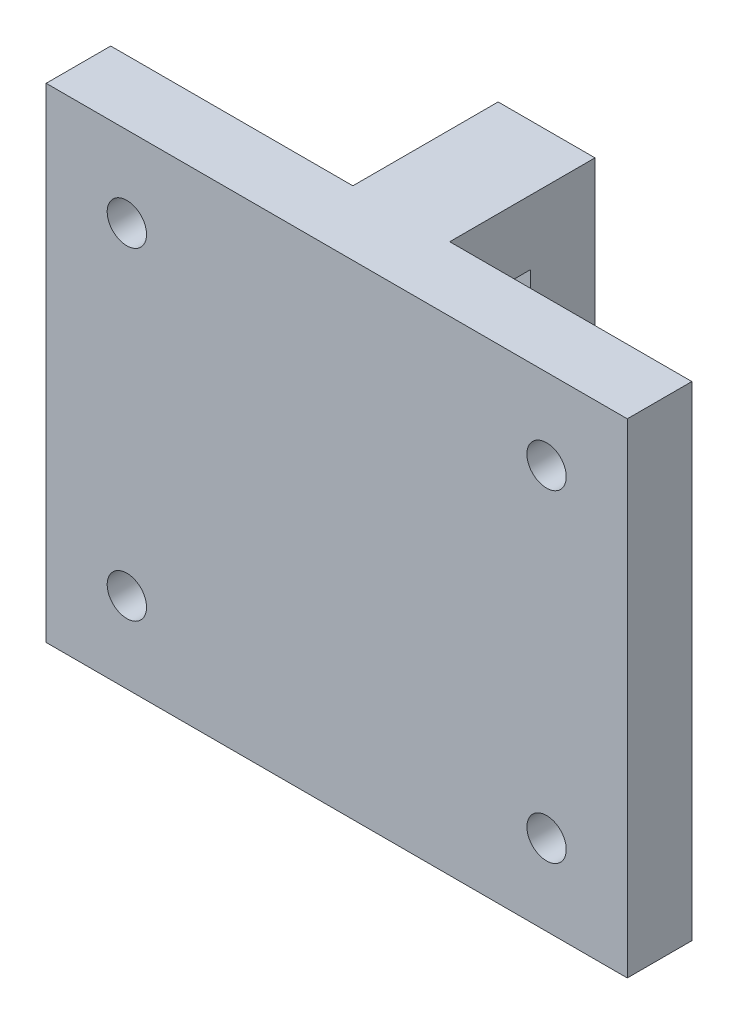
SolidWorks part; units mm, degrees
ref_plane "Front Plane" through (0, 0, 0) normal (0, 0, 1) x (1, 0, 0)
ref_plane "Top Plane" through (0, 0, 0) normal (0, 1, 0) x (1, 0, 0)
ref_plane "Right Plane" through (0, 0, 0) normal (1, 0, 0) x (0, 0, -1)
sketch "Sketch1" plane through (0, 0, 0) normal (1, 0, 0) x (0, 0, -1)
  line L1 (0, 0) -> (4, 0)
  line L2 (0, 0) -> (0, 30)
  line L3 (0, 30) -> (13, 30)
  line L4 (4, 0) -> (4, 26)
  line L5 (0, 30) -> (13, 30)
  line L7 (4, 26) -> (9, 26)
  line L8 (13, 30) -> (13, 16)
  line L10 (13, 30) -> (13, 16)
  line L11 (13, 16) -> (9, 16)
  line L12 (9, 26) -> (9, 16)
  dimension "D1" = 4
  dimension "D2" = 4
  dimension "D3" = 4
  dimension "D4" = 5
  dimension "D5" = 30
  dimension "D6" = 10
extrude "Boss-Extrude1" add sketch "Sketch1" along normal mid plane 6 contours L7 L12 L11 L8 L3 L2 L1 L4
sketch "Sketch2" plane through (0, 0, 0) normal (0, 0, 1) x (1, 0, 0)
  line L0 (3, 30) -> (-3, 30) construction
  line L1 (-18, 30) -> (18, 30)
  line L2 (-18, 30) -> (-18, 0)
  line L3 (-18, 0) -> (18, 0)
  line L4 (18, 30) -> (18, 0)
  line L5 (-3, 0) -> (-3, 30) construction
  line L6 (3, 0) -> (3, 30) construction
  dimension "D1" = 15
  dimension "D2" = 15
  dimension "D3" = 30
extrude "Boss-Extrude2" add sketch "Sketch2" against normal blind 4
sketch "Sketch3" plane through (0, 0, -4) normal (0, 0, -1) x (-1, 0, 0)
  line L0 (-18, 0) -> (-18, 30) construction
  line L1 (18, 0) -> (-18, 0) construction
  line L2 (-18, 30) -> (-3, 30) construction
  line L3 (18, 30) -> (18, 0) construction
  circle A0 centre (-13, 25) radius 1.5
  circle A1 centre (13, 25) radius 1.5
  circle A2 centre (-13, 5) radius 1.5
  circle A3 centre (13, 5) radius 1.5
  dimension "D1" = 3
  dimension "D2" = 5
  dimension "D3" = 5
  dimension "D4" = 5
  dimension "D5" = 5
hole_wizard "CSK for #2 Flat Head Machine Screw (100)1" positions "Sketch4" profile "Sketch5" countersink size "#2" standard "ANSI Inch" end condition through all
sketch "Sketch4" plane through (0, 0, -4) normal (0, 0, -1) x (-1, 0, 0)
  point P0 (-13, 25)
  point P3 (-13, 5)
  point P6 (13, 5)
  point P9 (13, 25)
sketch "Sketch5" plane through (13, 25, -4) normal (1, 0, 0) x (0, 1, 0)
  line L0 (0, 0) -> (0, 4)
  line L1 (0, 4) -> (1.2192, 4)
  line L2 (1.2192, 4) -> (1.2192, 0.8099)
  line L3 (1.2192, 0.8099) -> (2.1844, 0)
  line L5 (2.1844, 0) -> (0, 0)
  line L6 (-1.2192, 0.8099) -> (-2.1844, 0) construction
  line L11 (0, -6.35) -> (0, 107.95) construction
  dimension "Thru Hole Dia." = 2.4384
  dimension "Thru Hole Depth" = 4
  dimension "Near C'Sink Dia." = 4.3688
  dimension "Near C'Sink Angle" = 100
